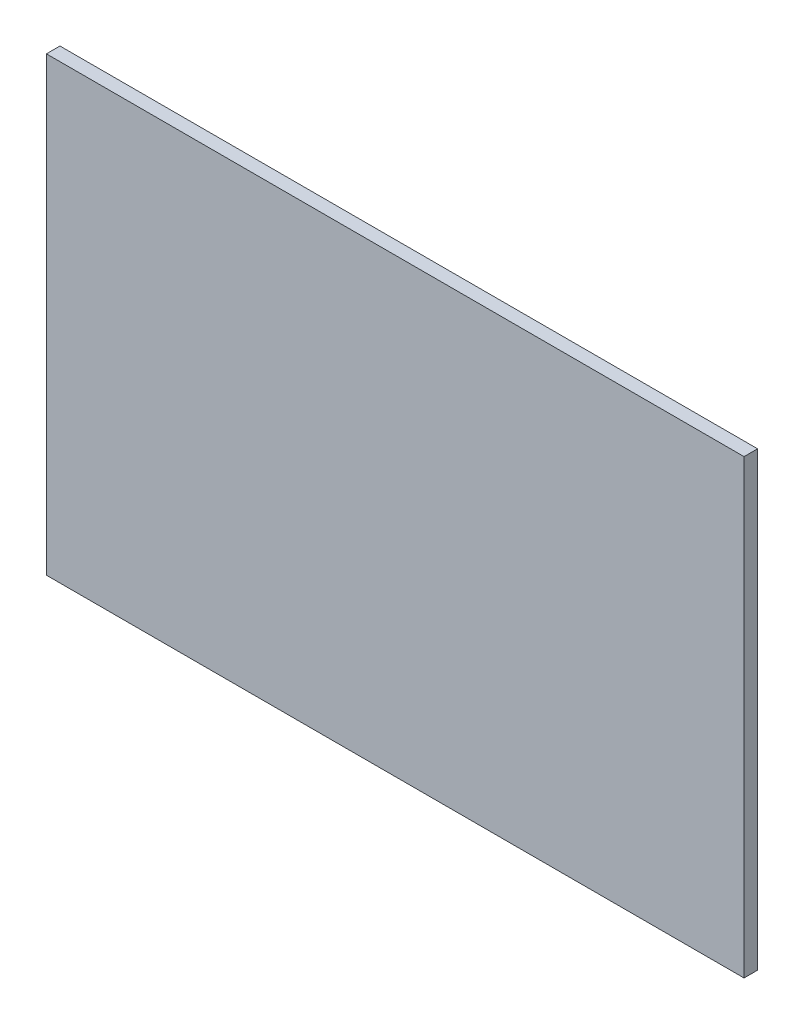
SolidWorks part; units mm, degrees
ref_plane "Plan de face" through (0, 0, 0) normal (0, 0, 1) x (1, 0, 0)
ref_plane "Plan de dessus" through (0, 0, 0) normal (0, 1, 0) x (1, 0, 0)
ref_plane "Plan de droite" through (0, 0, 0) normal (1, 0, 0) x (0, 0, -1)
sketch "Esquisse1" plane through (0, 0, 0) normal (0, 0, 1) x (1, 0, 0)
  line L1 (-151.5675, 208.3044) -> (-306.0675, 208.3044)
  line L2 (-151.5675, 208.3044) -> (-151.5675, 108.3044)
  line L3 (-151.5675, 108.3044) -> (-306.0675, 108.3044)
  line L4 (-306.0675, 208.3044) -> (-306.0675, 108.3044)
  dimension "D1" = 100
  dimension "D2" = 154.5
extrude "Boss.-Extru.1" add sketch "Esquisse1" along normal blind 3
